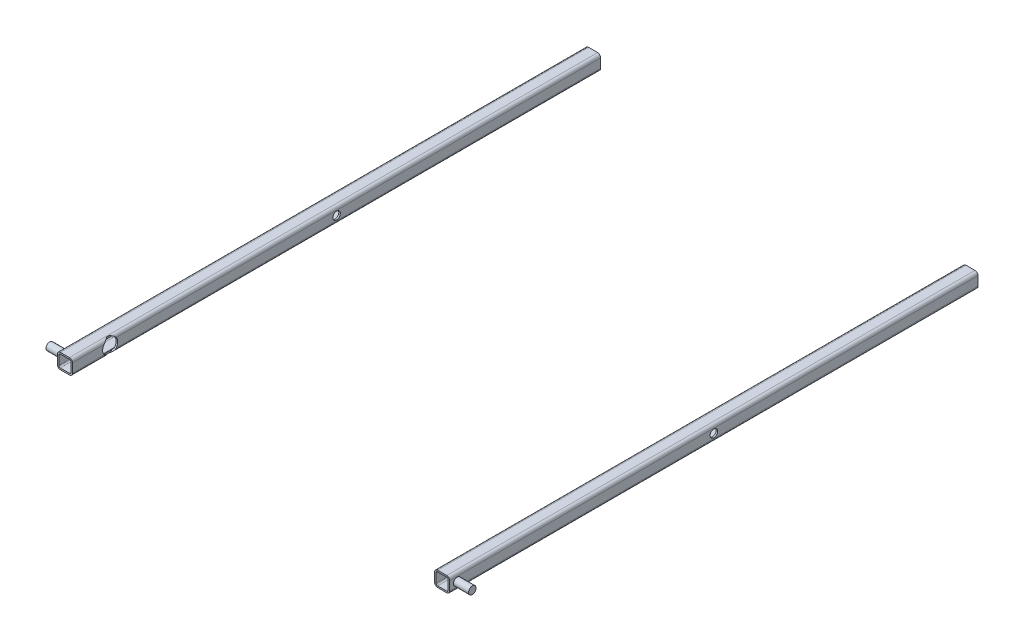
SolidWorks part; units mm, degrees
ref_plane "Front Plane" through (0, 0, 0) normal (0, 0, 1) x (1, 0, 0)
ref_plane "Top Plane" through (0, 0, 0) normal (0, 1, 0) x (1, 0, 0)
ref_plane "Right Plane" through (0, 0, 0) normal (1, 0, 0) x (0, 0, -1)
sketch "Sketch1" plane through (0, 0, 0) normal (0, 1, 0) x (1, 0, 0)
  line L0 (0, 450) -> (0, -382.2714) construction
  line L2 (250, 450) -> (250, -250)
  line L4 (-250, 450) -> (-250, -250)
  point P0 (0, 0)
  dimension "D1" = 500
  dimension "D2" = 700
other "Square tube - configured 20 X 20 X 2(1)"
ref_plane "Plane1" through (-250, 0, -450) normal (0, 0, 1) x (1, 0, 0)
sketch "Sketch111" plane through (-250, 0, -450) normal (0, 0, 1) x (1, 0, 0)
  line L0 (-6, -8) -> (6, -8)
  line L1 (-8, -6) -> (-8, 6)
  line L2 (6, 8) -> (-6, 8)
  line L3 (8, 6) -> (8, -6)
  line L4 (-6, -10) -> (6, -10)
  line L5 (-10, -6) -> (-10, 6)
  line L6 (6, 10) -> (-6, 10)
  line L7 (10, 6) -> (10, -6)
  arc A0 (10, 6) -> (6, 10) centre (6, 6) ccw
  arc A1 (6, -10) -> (10, -6) centre (6, -6) ccw
  arc A2 (-10, -6) -> (-6, -10) centre (-6, -6) ccw
  arc A3 (-6, 10) -> (-10, 6) centre (-6, 6) ccw
  arc A4 (-6, 8) -> (-8, 6) centre (-6, 6) ccw
  arc A5 (8, 6) -> (6, 8) centre (6, 6) ccw
  arc A6 (6, -8) -> (8, -6) centre (6, -6) ccw
  arc A7 (-8, -6) -> (-6, -8) centre (-6, -6) ccw
  point P0 (-10, 0)
  point P1 (10, 0)
  point P2 (0, 10)
  point P3 (0, -10)
  point P4 (0, 0)
  point P5 (-10, -10)
  point P6 (10, -10)
  point P7 (10, 10)
  point P8 (-10, 10)
  point P33 (0, 0)
  dimension "D1" = 4
  dimension "Thickness" = 2
  dimension "V_leg" = 20
sketch "Sketch15" plane through (0, 0, 0) normal (1, 0, 0) x (0, 0, -1)
  line L0 (-250, 0) -> (450, 0) construction
  line L1 (-250, -6) -> (-250, 6) construction
  line L2 (450, -6) -> (450, 6) construction
  circle A0 centre (100, 0) radius 5
  dimension "D1" = 10
extrude "Cut-Extrude1" cut sketch "Sketch15" against normal through all both and the other way through all
sketch "Sketch16" plane through (-260, 0, 0) normal (-1, 0, 0) x (0, 0, 1)
  line L0 (250, -10) -> (-450, -10) construction
  line L1 (250, 6) -> (250, -6) construction
  circle A0 centre (240, 0) radius 5
  dimension "D2" = 10
  dimension "D1" = 10
  dimension "D3" = 10
extrude "Boss-Extrude2" add sketch "Sketch16" along normal blind 20 separate body
mirror "Mirror2" about plane through (0, 0, 0) normal (1, 0, 0) of "Boss-Extrude2"
sketch "Sketch13" plane through (240, 0, 0) normal (-1, 0, 0) x (0, 0, 1)
  line L0 (250, 6) -> (250, -6) construction
  circle A0 centre (200, 0) radius 10
  dimension "D1" = 50
extrude "Cut-Extrude3" cut sketch "Sketch13" against normal blind 2 and the other way blind 483 contours A0
